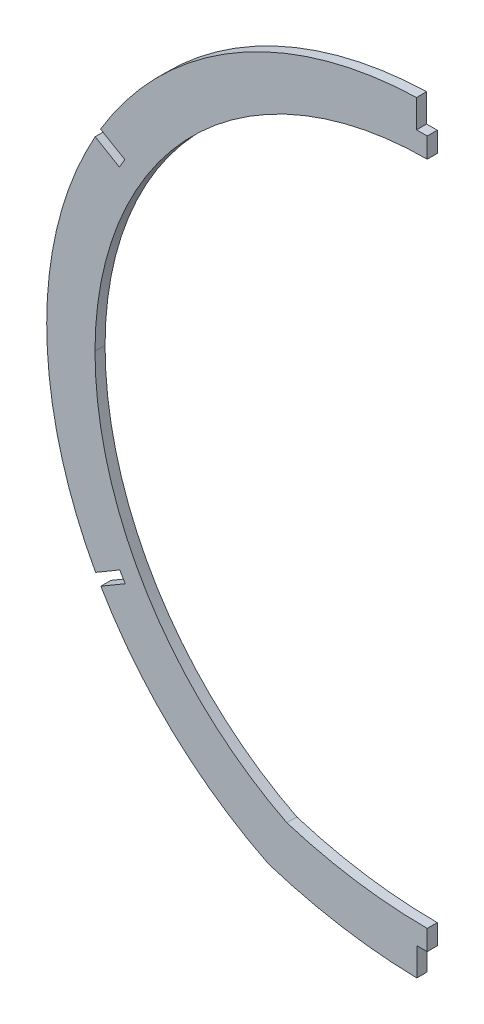
SolidWorks part; units mm, degrees
material "Plywood"
ref_plane "Front Plane" through (0, 0, 0) normal (0, 0, 1) x (1, 0, 0)
ref_plane "Top Plane" through (0, 0, 0) normal (0, 1, 0) x (1, 0, 0)
ref_plane "Right Plane" through (0, 0, 0) normal (1, 0, 0) x (0, 0, -1)
sketch "Sketch2" plane through (0, 0, 0) normal (0, 0, 1) x (1, 0, 0)
  line L0 (0, 0) -> (0.688, 245.4392) construction
  line L1 (-0.1309, -46.7153) -> (-0.2841, -101.3462) construction
  line L2 (0.0534, 19.05) -> (-169.3081, 19.05) construction
  line L3 (-72.7218, -93.726) -> (74.7111, -93.726) construction
  arc A1 (-120.0989, 19.05) -> (120.2036, 18.3433) centre (0.0534, 19.05) cw
  arc A2 (-120.0989, 19.05) -> (-50.0584, -93.726) centre (5.7147, 19.05) ccw
  arc A3 (-50.0584, -93.726) -> (50.1388, -93.726) centre (0.0402, 63.5) ccw
  arc A4 (120.2036, 18.3433) -> (50.1388, -93.726) centre (-5.6406, 19.0835) cw
  arc A5 (-104.8589, 19.05) -> (104.9639, 18.4329) centre (0.0534, 19.05) cw
  arc A6 (104.9639, 18.4329) -> (44.4049, -79.5534) centre (-5.6406, 19.0835) cw
  arc A7 (-44.324, -79.5535) -> (44.4049, -79.5534) centre (0.0402, 63.5) ccw
  arc A8 (-104.8589, 19.05) -> (-44.324, -79.5535) centre (5.7147, 19.05) ccw
  spline S0 degree 3 poles (-5521.0274, 5583.2546) (-1226.7801, 553.2855) (-196.9505, -260.8007) (69.4764, -82.4823) (75.8596, -77.7331) (81.7614, -72.3621) (85.2966, -68.8071) (85.996, -68.0862) (87.3792, -66.6243) (88.0639, -65.8824) (90.0847, -63.6371) (91.3894, -62.1126) (95.1787, -57.4581) (97.5389, -54.2471) (101.9343, -47.6137) (103.9694, -44.1914) (106.7765, -38.8981) (107.6712, -37.107) (109.3772, -33.4707) (110.1904, -31.6207) (112.481, -26.0415) (113.8153, -22.2742) (116.1105, -14.6467) (117.0712, -10.7866) (118.62, -2.9737) (119.208, 0.9791) (119.8028, 6.9796) (119.953, 8.9949) (120.1541, 13.0067) (120.2055, 15.0081) (120.2151, 20.9991) (119.8425, 28.9519) (118.7088, 36.835) (117.5685, 42.7208) (117.1399, 44.6783) (116.1841, 48.5842) (115.6559, 50.5346) (113.94, 56.3082) (112.6165, 60.0751) (109.6192, 67.4485) (107.9453, 71.055) (104.2453, 78.1066) (102.2192, 81.5518) (99.4588, 85.754) (98.8945, 86.5903) (97.7468, 88.2466) (97.1639, 89.0659) (95.3883, 91.4977) (94.1686, 93.0841) (90.4034, 97.7402) (87.752, 100.7072) (82.1689, 106.369) (79.2371, 109.0639) (74.6247, 112.8977) (73.0514, 114.1408) (70.6363, 115.9521) (69.821, 116.5478) (68.1799, 117.7153) (67.3537, 118.2875) (63.1947, 121.0918) (59.7778, 123.1535) (52.769, 126.9212) (49.1769, 128.6272) (41.816, 131.6806) (38.0473, 133.028) (33.2217, 134.4796) (32.2518, 134.758) (30.3116, 135.2882) (29.34, 135.5404) (26.4206, 136.2591) (24.4685, 136.6873) (18.5945, 137.8219) (14.6552, 138.3782) (6.7301, 139.0933) (2.7444, 139.252) (-2.2675, 139.1959) (-3.2714, 139.172) (-5.2821, 139.0983) (-6.2905, 139.0484) (-9.3072, 138.8606) (-11.3068, 138.6846) (-17.272, 138.0072) (-25.1357, 136.7069) (-32.823, 134.6274) (-38.5216, 132.7724) (-40.41, 132.1048) (-44.1641, 130.6694) (-46.0326, 129.9002) (-465.435, -55.3606) (264.7727, -2591.6725) (2155.1784, -7505.3224) knots -2.450405 -2.450405 -2.450405 -2.450405 0.03125 0.03125 0.0625 0.09375 0.09375 0.101563 0.101563 0.109375 0.109375 0.125 0.125 0.15625 0.15625 0.1875 0.1875 0.203125 0.203125 0.21875 0.21875 0.25 0.25 0.28125 0.28125 0.3125 0.3125 0.328125 0.328125 0.34375 0.34375 0.375 0.40625 0.40625 0.421875 0.421875 0.4375 0.4375 0.46875 0.46875 0.5 0.5 0.53125 0.53125 0.539063 0.539063 0.546875 0.546875 0.5625 0.5625 0.59375 0.59375 0.625 0.625 0.640625 0.640625 0.648438 0.648438 0.65625 0.65625 0.6875 0.6875 0.71875 0.71875 0.75 0.75 0.757813 0.757813 0.765625 0.765625 0.78125 0.78125 0.8125 0.8125 0.84375 0.84375 0.851563 0.851563 0.859375 0.859375 0.875 0.875 0.90625 0.9375 0.9375 0.953125 0.953125 0.96875 0.96875 4.508313 4.508313 4.508313 4.508313 only from (55.8537, -90.8749) to (-58.6671, 123.6507)
  spline S1 degree 3 poles (55.8537, -90.8749) (59.4151, -88.9779) (62.8499, -86.9173) (69.4764, -82.4823) (75.8596, -77.7331) (81.7614, -72.3621) (85.2966, -68.8071) (85.996, -68.0862) (87.3792, -66.6243) (88.0639, -65.8824) (90.0847, -63.6371) (91.3894, -62.1126) (95.1787, -57.4581) (97.5389, -54.2471) (101.9343, -47.6137) (103.9694, -44.1914) (106.7765, -38.8981) (107.6712, -37.107) (109.3772, -33.4707) (110.1904, -31.6207) (112.481, -26.0415) (113.8153, -22.2742) (116.1105, -14.6467) (117.0712, -10.7866) (118.62, -2.9737) (119.208, 0.9791) (119.8028, 6.9796) (119.953, 8.9949) (120.1541, 13.0067) (120.2055, 15.0081) (120.2151, 20.9991) (119.8425, 28.9519) (118.7088, 36.835) (117.5685, 42.7208) (117.1399, 44.6783) (116.1841, 48.5842) (115.6559, 50.5346) (113.94, 56.3082) (112.6165, 60.0751) (109.6192, 67.4485) (107.9453, 71.055) (104.2453, 78.1066) (102.2192, 81.5518) (99.4588, 85.754) (98.8945, 86.5903) (97.7468, 88.2466) (97.1639, 89.0659) (95.3883, 91.4977) (94.1686, 93.0841) (90.4034, 97.7402) (87.752, 100.7072) (82.1689, 106.369) (79.2371, 109.0639) (74.6247, 112.8977) (73.0514, 114.1408) (70.6363, 115.9521) (69.821, 116.5478) (68.1799, 117.7153) (67.3537, 118.2875) (63.1947, 121.0918) (59.7778, 123.1535) (52.769, 126.9212) (49.1769, 128.6272) (41.816, 131.6806) (38.0473, 133.028) (33.2217, 134.4796) (32.2518, 134.758) (30.3116, 135.2882) (29.34, 135.5404) (26.4206, 136.2591) (24.4685, 136.6873) (18.5945, 137.8219) (14.6552, 138.3782) (6.7301, 139.0933) (2.7444, 139.252) (-2.2675, 139.1959) (-3.2714, 139.172) (-5.2821, 139.0983) (-6.2905, 139.0484) (-9.3072, 138.8606) (-11.3068, 138.6846) (-17.272, 138.0072) (-25.1357, 136.7069) (-32.823, 134.6274) (-38.5216, 132.7724) (-40.41, 132.1048) (-44.1641, 130.6694) (-46.0326, 129.9002) (-51.5624, 127.4576) (-55.1595, 125.6458) (-58.6671, 123.6507) knots 0 0 0 0 0.03125 0.03125 0.0625 0.09375 0.09375 0.101563 0.101563 0.109375 0.109375 0.125 0.125 0.15625 0.15625 0.1875 0.1875 0.203125 0.203125 0.21875 0.21875 0.25 0.25 0.28125 0.28125 0.3125 0.3125 0.328125 0.328125 0.34375 0.34375 0.375 0.40625 0.40625 0.421875 0.421875 0.4375 0.4375 0.46875 0.46875 0.5 0.5 0.53125 0.53125 0.539063 0.539063 0.546875 0.546875 0.5625 0.5625 0.59375 0.59375 0.625 0.625 0.640625 0.640625 0.648438 0.648438 0.65625 0.65625 0.6875 0.6875 0.71875 0.71875 0.75 0.75 0.757813 0.757813 0.765625 0.765625 0.78125 0.78125 0.8125 0.8125 0.84375 0.84375 0.851563 0.851563 0.859375 0.859375 0.875 0.875 0.90625 0.9375 0.9375 0.953125 0.953125 0.96875 0.96875 1 1 1 1 construction
  spline S2 degree 3 poles (5694.5744, -5369.3669) (1292.3799, -516.6509) (187.1926, 314.492) (-76.9523, 111.0297) (-81.0984, 107.3558) (-85.9766, 102.3921) (-86.9369, 101.3807) (-88.8267, 99.3202) (-89.7577, 98.2691) (-92.4915, 95.0728) (-94.2304, 92.8907) (-99.2026, 86.1952) (-102.1931, 81.5333) (-106.1993, 74.2476) (-107.4545, 71.77) (-109.2154, 67.9791) (-109.782, 66.7031) (-110.874, 64.1258) (-111.4002, 62.8224) (-113.9097, 56.2871) (-115.5417, 50.9767) (-118.0823, 40.1978) (-118.9908, 34.7292) (-119.6657, 27.7928) (-119.7775, 26.4005) (-119.9543, 23.6055) (-120.0192, 22.2016) (-120.1418, 18.0057) (-120.1286, 15.2199) (-119.8102, 6.8959) (-119.2278, 1.3912) (-117.8014, -6.7994) (-117.2335, -9.5184) (-116.2404, -13.58) (-115.8858, -14.9311) (-115.1288, -17.6274) (-114.7258, -18.9739) (-112.6063, -25.6411) (-108.5276, -35.9696) (-103.1136, -45.6397) (-99.3011, -51.4722) (-98.5171, -52.628) (-96.9053, -54.9182) (-96.0765, -56.0537) (-93.5433, -59.4015) (-91.7865, -61.5635) (-86.3167, -67.8444) (-82.4051, -71.759) (-76.1398, -77.2217) (-73.9848, -78.9742) (-70.6503, -81.498) (-69.5218, -82.3217) (-67.2303, -83.9337) (-66.0665, -84.7222) (540.7318, -480.5341) (3882.3497, 5108.7967) (222.2795, -4616.5222) knots -3.63779 -3.63779 -3.63779 -3.63779 0.0625 0.0625 0.125 0.125 0.140625 0.140625 0.15625 0.15625 0.1875 0.1875 0.25 0.25 0.28125 0.28125 0.296875 0.296875 0.3125 0.3125 0.375 0.375 0.4375 0.4375 0.453125 0.453125 0.46875 0.46875 0.5 0.5 0.5625 0.5625 0.59375 0.59375 0.609375 0.609375 0.625 0.625 0.6875 0.75 0.75 0.765625 0.765625 0.78125 0.78125 0.8125 0.8125 0.875 0.875 0.90625 0.90625 0.921875 0.921875 0.9375 0.9375 9.012836 9.012836 9.012836 9.012836 only from (-58.6671, 123.6507) to (-50.3455, -93.5936)
  spline S3 degree 3 poles (-4578.1193, 6360.5009) (1102.8247, -3189.0685) (1357.3206, -1629.0846) (-2110.3169, 7551.2134) knots -196.711406 -196.711406 -196.711406 -196.711406 209.883914 209.883914 209.883914 209.883914 only from (49.819, -93.8744) to (55.8537, -90.8749)
  spline S4 degree 3 poles (49.819, -93.8744) (51.8584, -92.9316) (53.87, -91.9317) (55.8537, -90.8749) knots 0 0 0 0 1 1 1 1 construction
  spline S5 degree 3 poles (-58.6671, 123.6507) (-63.5487, 120.874) (-68.1774, 117.7887) (-76.9523, 111.0297) (-81.0984, 107.3558) (-85.9766, 102.3921) (-86.9369, 101.3807) (-88.8267, 99.3202) (-89.7577, 98.2691) (-92.4915, 95.0728) (-94.2304, 92.8907) (-99.2026, 86.1952) (-102.1931, 81.5333) (-106.1993, 74.2476) (-107.4545, 71.77) (-109.2154, 67.9791) (-109.782, 66.7031) (-110.874, 64.1258) (-111.4002, 62.8224) (-113.9097, 56.2871) (-115.5417, 50.9767) (-118.0823, 40.1978) (-118.9908, 34.7292) (-119.6657, 27.7928) (-119.7775, 26.4005) (-119.9543, 23.6055) (-120.0192, 22.2016) (-120.1418, 18.0057) (-120.1286, 15.2199) (-119.8102, 6.8959) (-119.2278, 1.3912) (-117.8014, -6.7994) (-117.2335, -9.5184) (-116.2404, -13.58) (-115.8858, -14.9311) (-115.1288, -17.6274) (-114.7258, -18.9739) (-112.6063, -25.6411) (-108.5276, -35.9696) (-103.1136, -45.6397) (-99.3011, -51.4722) (-98.5171, -52.628) (-96.9053, -54.9182) (-96.0765, -56.0537) (-93.5433, -59.4015) (-91.7865, -61.5635) (-86.3167, -67.8444) (-82.4051, -71.759) (-76.1398, -77.2217) (-73.9848, -78.9742) (-70.6503, -81.498) (-69.5218, -82.3217) (-67.2303, -83.9337) (-66.0665, -84.7222) (-60.2073, -88.5441) (-55.3561, -91.2432) (-50.3455, -93.5936) knots 0 0 0 0 0.0625 0.0625 0.125 0.125 0.140625 0.140625 0.15625 0.15625 0.1875 0.1875 0.25 0.25 0.28125 0.28125 0.296875 0.296875 0.3125 0.3125 0.375 0.375 0.4375 0.4375 0.453125 0.453125 0.46875 0.46875 0.5 0.5 0.5625 0.5625 0.59375 0.59375 0.609375 0.609375 0.625 0.625 0.6875 0.75 0.75 0.765625 0.765625 0.78125 0.78125 0.8125 0.8125 0.875 0.875 0.90625 0.90625 0.921875 0.921875 0.9375 0.9375 1 1 1 1 construction
  spline S6 degree 3 poles (-1759.0643, 7695.5768) (129.301, 75.0658) (104.9025, -75.6984) (45.8458, -95.3665) (44.8322, -95.6594) (41.7708, -96.4587) (39.7032, -96.8873) (35.5384, -97.6293) (33.4392, -97.9405) (29.2422, -98.4783) (27.1412, -98.7049) (20.8322, -99.2882) (16.6185, -99.55) (8.1799, -99.8877) (3.9548, -99.9623) (-4.5058, -99.9387) (-8.734, -99.8405) (-17.1695, -99.4557) (-21.3793, -99.1705) (-27.6778, -98.553) (-29.7745, -98.3152) (-33.9608, -97.7556) (-36.0504, -97.4344) (-39.177, -96.8603) (-40.2191, -96.653) (-42.292, -96.1992) (-43.3225, -95.953) (-45.3676, -95.407) (-46.3821, -95.1076) (-105.8729, -74.9194) (-124.4058, 77.5041) (2082.3243, 7613.4914) knots -1.777254 -1.777254 -1.777254 -1.777254 0.03125 0.03125 0.0625 0.0625 0.125 0.125 0.1875 0.1875 0.25 0.25 0.375 0.375 0.5 0.5 0.625 0.625 0.75 0.75 0.8125 0.8125 0.875 0.875 0.90625 0.90625 0.9375 0.9375 0.96875 0.96875 2.792352 2.792352 2.792352 2.792352 only from (49.8185, -93.8746) to (-50.3451, -93.5938)
  spline S7 degree 3 poles (49.8185, -93.8746) (48.8452, -94.325) (47.8521, -94.6984) (45.8458, -95.3665) (44.8322, -95.6594) (41.7708, -96.4587) (39.7032, -96.8873) (35.5384, -97.6293) (33.4392, -97.9405) (29.2422, -98.4783) (27.1412, -98.7049) (20.8322, -99.2882) (16.6185, -99.55) (8.1799, -99.8877) (3.9548, -99.9623) (-4.5058, -99.9387) (-8.734, -99.8405) (-17.1695, -99.4557) (-21.3793, -99.1705) (-27.6778, -98.553) (-29.7745, -98.3152) (-33.9608, -97.7556) (-36.0504, -97.4344) (-39.177, -96.8603) (-40.2191, -96.653) (-42.292, -96.1992) (-43.3225, -95.953) (-45.3676, -95.407) (-46.3821, -95.1076) (-48.3867, -94.4274) (-49.3773, -94.0483) (-50.3451, -93.5938) knots 0 0 0 0 0.03125 0.03125 0.0625 0.0625 0.125 0.125 0.1875 0.1875 0.25 0.25 0.375 0.375 0.5 0.5 0.625 0.625 0.75 0.75 0.8125 0.8125 0.875 0.875 0.90625 0.90625 0.9375 0.9375 0.96875 0.96875 1 1 1 1 construction
  spline S8 degree 1 poles (44.4895, -82.3468) (49.8828, -79.6661) knots 0 0 1 1 construction
  spline S9 degree 1 poles (49.8828, -79.6661) (-52.388, 112.6115) knots 0 0 1 1 construction
  spline S10 degree 1 poles (-52.388, 112.6115) (-44.952, -82.0958) knots 0 0 1 1 construction
  spline S11 degree 3 poles (44.4895, -82.3468) (44.9451, -82.1361) (45.8533, -81.7084) (47.2062, -81.0479) (48.5497, -80.3682) (49.4396, -79.9022) (49.8828, -79.6661) knots 0 0 0 0 0.250007 0.500014 0.750021 1.000028 1.000028 1.000028 1.000028 construction
  spline S12 degree 3 poles (49.8828, -79.6661) (51.4682, -78.8216) (54.6039, -77.0481) (60.6329, -73.2256) (67.7713, -67.9145) (75.6946, -60.7068) (85.376, -49.946) (92.2499, -39.5527) (97.0635, -29.9209) (99.9774, -23.2906) (102.9687, -14.8438) (105.5551, -4.452) (106.8747, 4.4138) (107.4138, 11.642) (107.598, 18.8242) (107.1791, 27.7507) (105.6575, 38.3493) (103.0737, 48.9109) (99.5091, 59.0529) (95.0071, 68.7524) (90.4672, 76.4728) (86.3465, 82.4205) (79.7918, 90.9419) (71.0678, 99.805) (59.5047, 108.4813) (50.3361, 114.0108) (40.7123, 118.5824) (32.2831, 121.5955) (25.3334, 123.4944) (18.366, 125.0225) (9.571, 126.2643) (-1.0997, 126.6912) (-11.9104, 126.0185) (-22.4327, 124.2743) (-36.1547, 120.5693) (-46.1487, 116.1604) (-52.388, 112.6115) knots 0 0 0 0 0.015625 0.03125 0.0625 0.09375 0.125 0.1875 0.203125 0.21875 0.25 0.28125 0.3125 0.328125 0.34375 0.375 0.40625 0.4375 0.46875 0.5 0.53125 0.546875 0.5625 0.625 0.65625 0.6875 0.71875 0.75 0.765625 0.78125 0.8125 0.84375 0.875 0.90625 0.9375 1 1 1 1 construction
  spline S13 degree 3 poles (-52.388, 112.6115) (-54.5585, 111.3769) (-58.8261, 108.7475) (-66.8816, 102.9693) (-76.1597, 94.757) (-85.9932, 83.258) (-92.681, 72.8203) (-97.1816, 63.9424) (-101.112, 54.6656) (-104.776, 42.7383) (-106.8137, 30.488) (-107.4512, 20.4245) (-107.4028, 10.4189) (-106.3564, 0.5368) (-104.3212, -9.2152) (-101.5955, -18.9231) (-97.0158, -30.5128) (-90.9605, -41.334) (-85.1677, -49.567) (-78.8706, -57.3154) (-71.8665, -64.3232) (-64.1621, -70.5906) (-57.9948, -74.9291) (-51.5954, -78.7902) (-47.193, -81.0446) (-44.952, -82.0958) knots 0 0 0 0 0.03125 0.0625 0.125 0.1875 0.25 0.28125 0.3125 0.375 0.4375 0.46875 0.5 0.5625 0.59375 0.625 0.6875 0.75 0.78125 0.8125 0.875 0.90625 0.9375 0.96875 1 1 1 1 construction
  spline S14 degree 1 poles (44.4849, -82.3489) (-44.9469, -82.0982) knots 0 0 1 1 construction
  spline S15 degree 3 poles (44.4849, -82.3489) (44.3746, -82.3999) (44.1627, -82.4934) (43.6492, -82.7012) (42.8561, -82.9839) (41.7841, -83.3184) (40.2245, -83.7477) (38.1103, -84.2445) (35.4106, -84.7656) (32.6063, -85.224) (28.7759, -85.7537) (23.885, -86.2821) (17.9201, -86.7432) (11.8971, -87.0512) (5.8396, -87.2261) (-2.2666, -87.2864) (-10.3738, -87.0974) (-18.3985, -86.6419) (-24.3556, -86.1481) (-29.2377, -85.5934) (-33.056, -85.0443) (-35.8555, -84.5718) (-38.5671, -84.0318) (-40.6899, -83.5223) (-42.2517, -83.0828) (-43.3238, -82.7417) (-44.1147, -82.4546) (-44.6269, -82.2439) (-44.8373, -82.1497) (-44.9469, -82.0982) knots 0 0 0 0 0.007812 0.015625 0.03125 0.046875 0.0625 0.09375 0.125 0.15625 0.1875 0.25 0.3125 0.375 0.4375 0.5 0.625 0.6875 0.75 0.8125 0.84375 0.875 0.90625 0.9375 0.953125 0.96875 0.984375 0.992188 1 1 1 1 construction
  point P12 (-0.2802, -99.9505)
  dimension "D3" = 19.05
  dimension "D4" = 93.726
  dimension "D5" = 63.5
  dimension "D6" = 15.24
  dimension "D1" = 12.7
  dimension "D2" = 12.7
extrude "Boss-Extrude1" add sketch "Sketch2" along normal mid plane 3.175
sketch "Sketch3" plane through (0, 0, 0) normal (1, 0, 0) x (0, 0, -1)
  line L1 (-100.0568, 212.3798) -> (108.5889, 212.3798)
  line L2 (-100.0568, 212.3798) -> (-100.0568, -170.6472)
  line L3 (-100.0568, -170.6472) -> (108.5889, -170.6472)
  line L4 (108.5889, 212.3798) -> (108.5889, -170.6472)
extrude "Cut-Extrude1" cut sketch "Sketch3" along normal through all
sketch "Sketch4" plane through (0, 0, 1.5875) normal (0, 0, 1) x (1, 0, 0)
  line L0 (0, 0) -> (0, 123.9623) construction
  line L1 (0, 123.9623) -> (0, 130.3123) construction
  line L2 (-3.3782, 130.3123) -> (3.3782, 130.3123)
  line L3 (0, 130.3123) -> (0, 143.0123)
  line L4 (3.3782, 130.3123) -> (3.3782, 143.0123)
  line L5 (-3.3782, 143.0123) -> (3.3782, 143.0123)
  line L6 (90.8212, 71.4752) -> (96.2977, 74.6892) construction
  line L7 (95.4428, 76.146) -> (97.1526, 73.2325)
  line L8 (90.8212, 71.4752) -> (0, 18.1749) construction
  line L9 (95.4428, 76.146) -> (106.3959, 82.5741)
  line L10 (97.1526, 73.2325) -> (108.1057, 79.6605)
  line L11 (106.3959, 82.5741) -> (108.1057, 79.6605)
  line L12 (90.7135, -35.0622) -> (96.19, -38.2762) construction
  line L13 (90.7135, -35.0622) -> (0, 18.1749) construction
  line L14 (95.3351, -39.733) -> (97.045, -36.8194)
  line L15 (95.3351, -39.733) -> (106.2882, -46.161)
  line L16 (97.045, -36.8194) -> (107.998, -43.2475)
  line L17 (106.2882, -46.161) -> (107.998, -43.2475)
  line L18 (0, 0) -> (0, -86.2748) construction
  line L19 (0, -86.2748) -> (0, -92.6248) construction
  line L20 (-3.302, -92.6248) -> (3.302, -92.6248)
  line L21 (0, -92.6248) -> (0, -105.3248)
  line L22 (3.302, -92.6248) -> (3.302, -105.3248)
  line L23 (-3.302, -105.3248) -> (3.302, -105.3248)
  line L24 (-90.7135, -35.0622) -> (0, 18.1749) construction
  line L25 (-90.7135, -35.0622) -> (-96.19, -38.2762) construction
  line L26 (-90.8212, 71.4752) -> (0, 18.1749) construction
  line L27 (-90.8212, 71.4752) -> (-96.2977, 74.6892) construction
  line L28 (-3.302, -92.6248) -> (-3.302, -105.3248)
  line L29 (-106.2882, -46.161) -> (-107.998, -43.2475)
  line L30 (-97.045, -36.8194) -> (-107.998, -43.2475)
  line L31 (-95.3351, -39.733) -> (-106.2882, -46.161)
  line L32 (-95.3351, -39.733) -> (-97.045, -36.8194)
  line L33 (-106.3959, 82.5741) -> (-108.1057, 79.6605)
  line L34 (-97.1526, 73.2325) -> (-108.1057, 79.6605)
  line L35 (-95.4428, 76.146) -> (-106.3959, 82.5741)
  line L36 (-95.4428, 76.146) -> (-97.1526, 73.2325)
  line L37 (-3.3782, 130.3123) -> (-3.3782, 143.0123)
  point P2 (96.2977, 74.6892)
  point P10 (96.19, -38.2762)
  arc M24 (-50.0584, -93.726) -> (0, -101.5148) centre (0.0402, 63.5) ccw
  line M25 (0, -101.5148) -> (0, -86.2748)
  line M29 (0, 123.9623) -> (0, 139.2023)
  arc M30 (0, 139.2023) -> (-120.0989, 19.05) centre (0.0534, 19.05) ccw
  arc M31 (-120.0989, 19.05) -> (-50.0584, -93.726) centre (5.7147, 19.05) ccw
  dimension "D1" = 123.9623
  dimension "D2" = 6.35
  dimension "D3" = 3.3782
  dimension "D4" = 12.7
  dimension "D5" = 59.593
  dimension "D6" = 18.1749
  dimension "D7" = 105.3062
  dimension "D8" = 6.35
  dimension "D9" = 3.3782
  dimension "D10" = 12.7
  dimension "D11" = 59.593
  dimension "D12" = 105.1814
  dimension "D13" = 6.35
  dimension "D14" = 12.7
  dimension "D15" = 3.3782
  dimension "D16" = 6.35
  dimension "D17" = 86.2748
  dimension "D18" = 3.302
  dimension "D19" = 12.7
extrude "Cut-Extrude2" cut sketch "Sketch4" against normal through all contours L36 L35 L34 M30 | L37 L2 M29 M30 | L31 L32 L30 M31 | L20 L28 M24 M25
